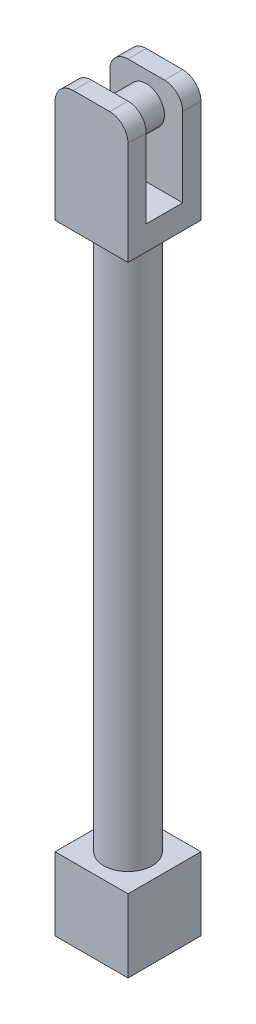
SolidWorks part; units mm, degrees
ref_plane "Front Plane" through (0, 0, 0) normal (0, 0, 1) x (1, 0, 0)
ref_plane "Top Plane" through (0, 0, 0) normal (0, 1, 0) x (1, 0, 0)
ref_plane "Right Plane" through (0, 0, 0) normal (1, 0, 0) x (0, 0, -1)
sketch "Sketch1" plane through (0, 0, 0) normal (0, 1, 0) x (1, 0, 0)
  line L1 (-15, 15) -> (15, 15)
  line L2 (-15, 15) -> (-15, -15)
  line L3 (-15, -15) -> (15, -15)
  line L4 (15, 15) -> (15, -15)
  line L5 (-15, 15) -> (15, -15) construction
  line L6 (-15, -15) -> (15, 15) construction
  point P0 (0, 0)
  dimension "D1" = 30
  dimension "D2" = 30
extrude "Boss-Extrude1" add sketch "Sketch1" along normal blind 30
sketch "Sketch2" plane through (0, 30, 0) normal (0, 1, 0) x (1, 0, 0)
  circle A0 centre (0, 0) radius 10
  dimension "D1" = 20
extrude "Boss-Extrude2" add sketch "Sketch2" along normal blind 225
sketch "Sketch3" plane through (0, 255, 0) normal (0, 1, 0) x (1, 0, 0)
  line L1 (-15, 15) -> (15, 15)
  line L2 (-15, 15) -> (-15, -15)
  line L3 (-15, -15) -> (15, -15)
  line L4 (15, 15) -> (15, -15)
  line L5 (-15, 15) -> (15, -15) construction
  line L6 (-15, -15) -> (15, 15) construction
  point P0 (0, 0)
  dimension "D1" = 30
  dimension "D2" = 30
extrude "Boss-Extrude3" add sketch "Sketch3" along normal blind 50
sketch "Sketch4" plane through (0, 305, 0) normal (0, 1, 0) x (1, 0, 0)
  line L0 (-15, 15) -> (-15, -15) construction
  line L1 (-15, 7.5) -> (15, 7.5)
  line L2 (-15, 7.5) -> (-15, -7.5)
  line L3 (-15, -7.5) -> (15, -7.5)
  line L4 (15, 7.5) -> (15, -7.5)
  line L5 (15, -15) -> (15, 15) construction
  line L6 (-15, -15) -> (15, -15) construction
  dimension "D1" = 15
  dimension "D2" = 7.5
extrude "Cut-Extrude1" cut sketch "Sketch4" against normal blind 40
sketch "Sketch5" plane through (0, 0, 7.5) normal (0, 0, -1) x (-1, 0, 0)
  line L0 (15, 305) -> (-15, 305) construction
  line L1 (15, 265) -> (15, 305) construction
  circle A0 centre (0, 292.5) radius 7.5
  dimension "D1" = 15
  dimension "D2" = 12.5
  dimension "D3" = 15
extrude "Boss-Extrude4" add sketch "Sketch5" along normal up to surface (15 mm away) up to face at (0, 285, -7.5)
fillet "Fillet1" radius 7.5 4 edges at (15, 305, -11.25) (15, 305, 11.25) (-15, 305, 11.25) (-15, 305, -11.25)
